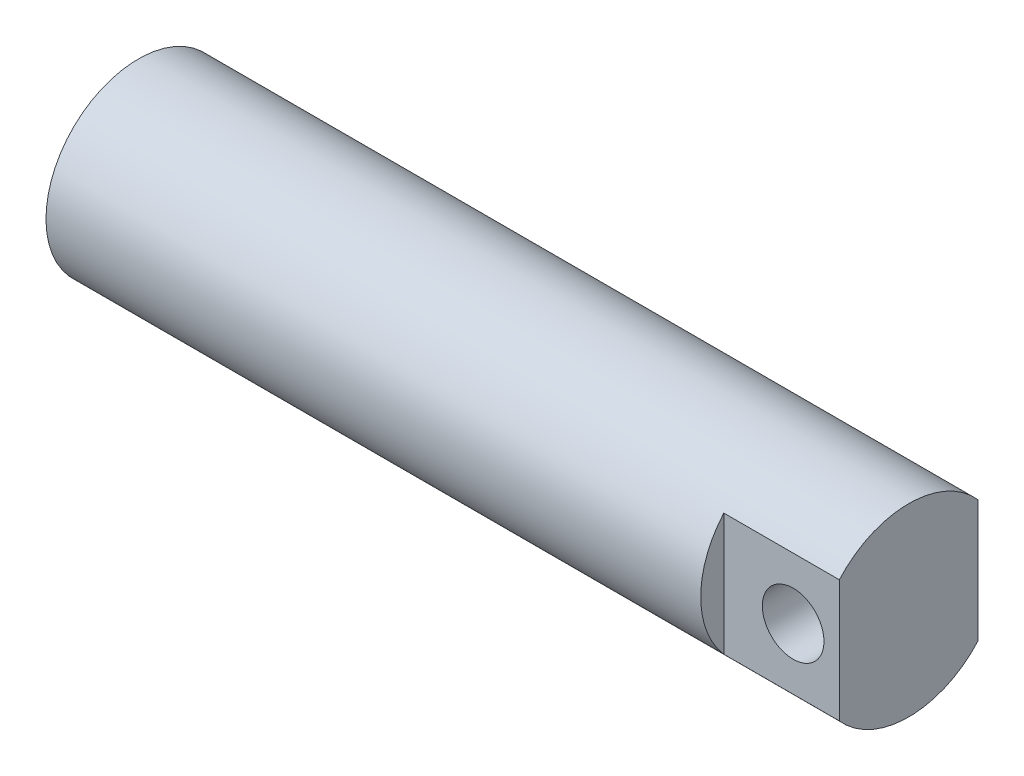
SolidWorks part; units mm, degrees
material "Alloy Steel"
ref_plane "Front Plane" through (0, 0, 0) normal (0, 0, 1) x (1, 0, 0)
ref_plane "Top Plane" through (0, 0, 0) normal (0, 1, 0) x (1, 0, 0)
ref_plane "Right Plane" through (0, 0, 0) normal (1, 0, 0) x (0, 0, -1)
sketch "Sketch2" plane through (0, 0, 0) normal (1, 0, 0) x (0, 0, -1)
  circle A0 centre (0, 0) radius 38.1
  dimension "D1" = 76.2
extrude "Boss-Extrude1" add sketch "Sketch2" along normal mid plane 317.5
sketch "Sketch3" plane through (158.75, 0, 0) normal (1, 0, 0) x (0, 0, -1)
  line L0 (0, 38.1) -> (0, -38.1) construction
  line L2 (-28.575, 25.2008) -> (-28.575, -25.2008)
  line L4 (28.575, 25.2008) -> (28.575, -25.2008)
  arc A0 (-28.575, 25.2008) -> (-28.575, -25.2008) centre (0, 0) ccw
  arc A1 (28.575, -25.2008) -> (28.575, 25.2008) centre (0, 0) ccw
  circle A2 centre (0, 0) radius 38.1 construction
  dimension "D1" = 76.2
  dimension "D2" = 28.575
extrude "Cut-Extrude1" cut sketch "Sketch3" against normal blind 47.625
sketch "Sketch4" plane through (0, 0, 28.575) normal (0, 0, 1) x (1, 0, 0)
  line L0 (158.75, 0) -> (0, 0) construction
  line L1 (158.75, -25.2008) -> (158.75, 25.2008) construction
  circle A0 centre (139.7, 0) radius 12.7
  dimension "D1" = 25.4
  dimension "D2" = 19.05
extrude "Cut-Extrude2" cut sketch "Sketch4" against normal through all
